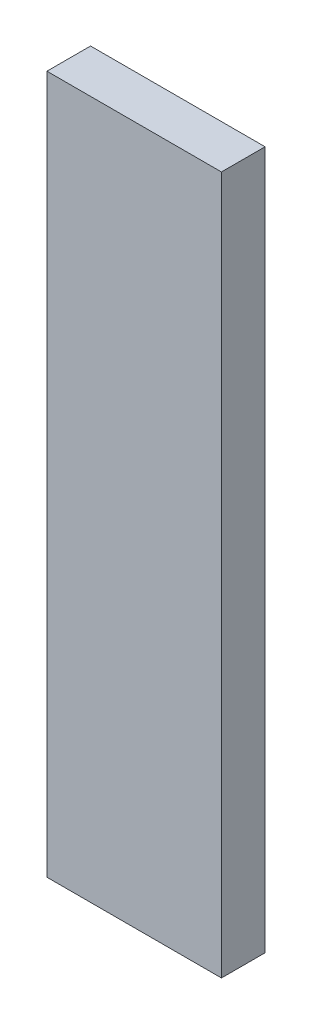
SolidWorks part; units mm, degrees
ref_plane "Front Plane" through (0, 0, 0) normal (0, 0, 1) x (1, 0, 0)
ref_plane "Top Plane" through (0, 0, 0) normal (0, 1, 0) x (1, 0, 0)
ref_plane "Right Plane" through (0, 0, 0) normal (1, 0, 0) x (0, 0, -1)
sketch "Sketch1" plane through (0, 0, 0) normal (0, 1, 0) x (1, 0, 0)
  line L1 (0, 0) -> (25.4, 0)
  line L2 (0, 0) -> (0, 6.35)
  line L3 (0, 6.35) -> (25.4, 6.35)
  line L4 (25.4, 0) -> (25.4, 6.35)
  dimension "D1" = 6.35
  dimension "D2" = 25.4
extrude "Boss-Extrude1" add sketch "Sketch1" along normal blind 101.6
